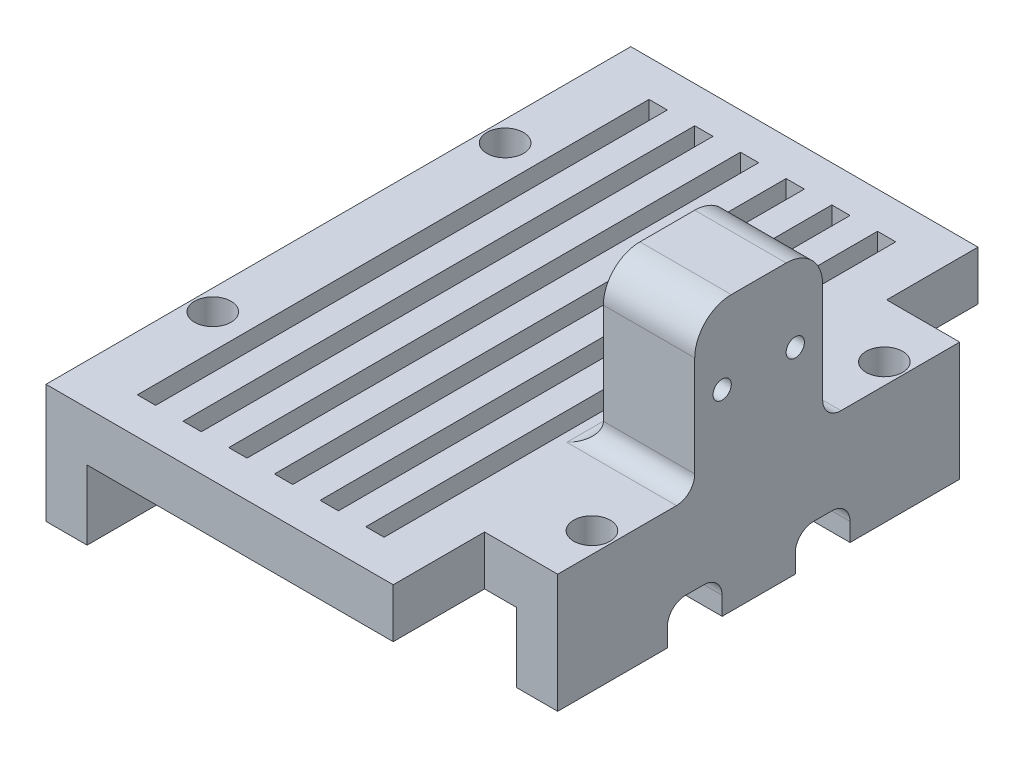
SolidWorks part; units mm, degrees
ref_plane "Front" through (0, 0, 0) normal (0, 0, 1) x (1, 0, 0)
ref_plane "Top" through (0, 0, 0) normal (0, 1, 0) x (1, 0, 0)
ref_plane "Right" through (0, 0, 0) normal (1, 0, 0) x (0, 0, -1)
sketch "草图1" plane through (0, 0, 0) normal (0, 1, 0) x (1, 0, 0)
  line L1 (11.5, -16) -> (-11.5, -16)
  line L2 (11.5, -16) -> (11.5, 16)
  line L3 (11.5, 16) -> (-11.5, 16)
  line L4 (-11.5, -16) -> (-11.5, 16)
  line L5 (11.5, -16) -> (-11.5, 16) construction
  line L6 (11.5, 16) -> (-11.5, -16) construction
  point P0 (0, 0)
  dimension "D1" = 32
  dimension "D2" = 23
extrude "凸台-拉伸1" add sketch "草图1" along normal blind 6.5
sketch "草图3" plane through (0, 0, 0) normal (0, -1, 0) x (1, 0, 0)
  line L0 (-11.5, 16) -> (11.5, 16) construction
  line L1 (9.25, -16) -> (-9.25, -16)
  line L2 (9.25, -16) -> (9.25, 16)
  line L3 (9.25, 16) -> (-9.25, 16)
  line L4 (-9.25, -16) -> (-9.25, 16)
  line L5 (9.25, -16) -> (-9.25, 16) construction
  line L6 (9.25, 16) -> (-9.25, -16) construction
  point P0 (0, 0)
  dimension "D1" = 18.5
extrude "切除-拉伸1" cut sketch "草图3" against normal blind 3.8
sketch "草图4" plane through (0, 0, 0) normal (0, -1, 0) x (1, 0, 0)
  line L0 (-26.5354, 0) -> (25.4999, 0) construction
  line L7 (-11.5, -16) -> (-11.5, 16) construction
  line L8 (11.5031, 2) -> (-11.5, 2)
  line L9 (11.5031, 2) -> (11.5031, 5)
  line L10 (11.5031, 5) -> (-11.5, 5)
  line L11 (-11.5, 2) -> (-11.5, 5)
  line L12 (11.5031, 2) -> (-11.5, 5) construction
  line L13 (11.5031, 5) -> (-11.5, 2) construction
  line L14 (11.5031, -5) -> (-11.5, -2) construction
  line L15 (11.5031, -2) -> (-11.5, -5) construction
  line L16 (-11.5, -2) -> (-11.5, -5)
  line L17 (11.5031, -5) -> (-11.5, -5)
  line L18 (11.5031, -2) -> (11.5031, -5)
  line L19 (11.5031, -2) -> (-11.5, -2)
  point P3 (0.0015, 3.5)
  point P14 (0.0015, -3.5)
  dimension "D1" = 3
  dimension "D2" = 7
extrude "切除-拉伸2" cut sketch "草图4" against normal blind 2
sketch "草图5" plane through (0, 0, 0) normal (0, -1, 0) x (1, 0, 0)
  line L0 (-23.3168, 0) -> (20.1561, 0) construction
  line L1 (0, -21.7438) -> (0, 24.7243) construction
  circle A0 centre (-10.375, -8) radius 0.6
  circle A1 centre (10.375, -8) radius 0.6
  circle A2 centre (10.375, 8) radius 0.6
  circle A3 centre (-10.375, 8) radius 0.6
  dimension "D1" = 1.2
  dimension "D2" = 20.75
  dimension "D3" = 16
extrude "切除-拉伸3" cut sketch "草图5" against normal through all
sketch "草图6" plane through (0, 6.5, 0) normal (0, 1, 0) x (1, 0, 0)
  line L0 (-17.124, 0) -> (19.2364, 0) construction
  line L1 (11.5, -16) -> (11.5, 16) construction
  line L2 (11.5, -3.5) -> (6.5, -3.5)
  line L3 (11.5, -3.5) -> (11.5, 3.5)
  line L4 (11.5, 3.5) -> (6.5, 3.5)
  line L5 (6.5, -3.5) -> (6.5, 3.5)
  line L6 (11.5, -3.5) -> (6.5, 3.5) construction
  line L7 (11.5, 3.5) -> (6.5, -3.5) construction
  point P3 (9, 0)
  dimension "D1" = 5
  dimension "D2" = 7
extrude "凸台-拉伸2" add sketch "草图6" along normal blind 8.5
fillet "圆角1" radius 1 8 edges at (10.375, 2, 5) (-10.375, 2, 5) (-10.375, 2, -2) (10.375, 2, -2) (10.375, 2, 2) (10.375, 2, -5) (-10.375, 2, 2) (-10.375, 2, -5)
sketch "草图7" plane through (11.5, 0, 0) normal (1, 0, 0) x (0, 0, -1)
  line L0 (0, 19.0946) -> (0, -7.7114) construction
  line L1 (-3.5, 15) -> (3.5, 15) construction
  circle A0 centre (-2, 10.75) radius 0.5
  circle A1 centre (2, 10.75) radius 0.5
  dimension "D1" = 1
  dimension "D2" = 4
  dimension "D3" = 4.25
extrude "切除-拉伸4" cut sketch "草图7" against normal through all
fillet "圆角2" radius 2 2 edges at (9, 15, 3.5) (9, 15, -3.5)
fillet "圆角3" radius 1 3 edges at (6.5, 6.5, 0) (9, 6.5, -3.5) (9, 6.5, 3.5)
sketch "草图8" plane through (0, 0, 0) normal (0, -1, 0) x (1, 0, 0)
  line L0 (-18.7042, 0) -> (26.5354, 0) construction
  line L1 (11.5, 16) -> (7.5, 16)
  line L2 (11.5, 16) -> (11.5, 11)
  line L3 (11.5, 11) -> (7.5, 11)
  line L4 (7.5, 16) -> (7.5, 11)
  line L5 (7.5, -16) -> (7.5, -11)
  line L6 (11.5, -11) -> (7.5, -11)
  line L7 (11.5, -16) -> (11.5, -11)
  line L8 (11.5, -16) -> (7.5, -16)
  dimension "D1" = 5
  dimension "D2" = 4
extrude "切除-拉伸5" cut sketch "草图8" against normal through all
sketch "草图9" plane through (0, 6.5, 0) normal (0, 1, 0) x (1, 0, 0)
  circle A0 centre (-10.375, 8) radius 1
  circle A1 centre (10.375, 8) radius 1
  circle A2 centre (10.375, 8) radius 0.6 construction
  circle A3 centre (-10.375, -8) radius 1
  circle A4 centre (10.375, -8) radius 1
  circle A5 centre (-10.375, -8) radius 0.6 construction
  circle A6 centre (10.375, -8) radius 0.6 construction
  dimension "D1" = 2
extrude "切除-拉伸6" cut sketch "草图9" against normal blind 3
sketch "草图10" plane through (0, 6.5, 0) normal (0, 1, 0) x (1, 0, 0)
  line L0 (-21.7427, 0) -> (25.1004, 0) construction
  line L1 (-11.5, 16) -> (-11.5, -16) construction
  line L2 (-7.5, -14) -> (-8.5, -14)
  line L3 (-7.5, -14) -> (-7.5, 14)
  line L4 (-7.5, 14) -> (-8.5, 14)
  line L5 (-8.5, -14) -> (-8.5, 14)
  line L6 (-7.5, -14) -> (-8.5, 14) construction
  line L7 (-7.5, 14) -> (-8.5, -14) construction
  line L8 (-5, -14) -> (-6, -14)
  line L9 (-5, -14) -> (-5, 14)
  line L10 (-5, 14) -> (-6, 14)
  line L11 (-6, -14) -> (-6, 14)
  line L12 (-5, -14) -> (-6, 14) construction
  line L13 (-5, 14) -> (-6, -14) construction
  line L14 (-2.5, -14) -> (-3.5, -14)
  line L15 (-2.5, -14) -> (-2.5, 14)
  line L16 (-2.5, 14) -> (-3.5, 14)
  line L17 (-3.5, -14) -> (-3.5, 14)
  line L18 (-2.5, -14) -> (-3.5, 14) construction
  line L19 (-2.5, 14) -> (-3.5, -14) construction
  line L20 (0, -14) -> (-1, -14)
  line L21 (0, -14) -> (0, 14)
  line L22 (0, 14) -> (-1, 14)
  line L23 (-1, -14) -> (-1, 14)
  line L24 (0, -14) -> (-1, 14) construction
  line L25 (0, 14) -> (-1, -14) construction
  line L26 (2.5, -14) -> (1.5, -14)
  line L27 (2.5, -14) -> (2.5, 14)
  line L28 (2.5, 14) -> (1.5, 14)
  line L29 (1.5, -14) -> (1.5, 14)
  line L30 (2.5, -14) -> (1.5, 14) construction
  line L31 (2.5, 14) -> (1.5, -14) construction
  line L32 (5, -14) -> (4, -14)
  line L33 (5, -14) -> (5, 14)
  line L34 (5, 14) -> (4, 14)
  line L35 (4, -14) -> (4, 14)
  line L36 (5, -14) -> (4, 14) construction
  line L37 (5, 14) -> (4, -14) construction
  point P3 (-8, 0)
  point P12 (-5.5, 0)
  point P17 (-3, 0)
  point P22 (-0.5, 0)
  point P27 (2, 0)
  point P32 (4.5, 0)
  dimension "D1" = 1
  dimension "D2" = 3.5
  dimension "D3" = 28
  dimension "D4" = 6
extrude "切除-拉伸7" cut sketch "草图10" against normal through all
